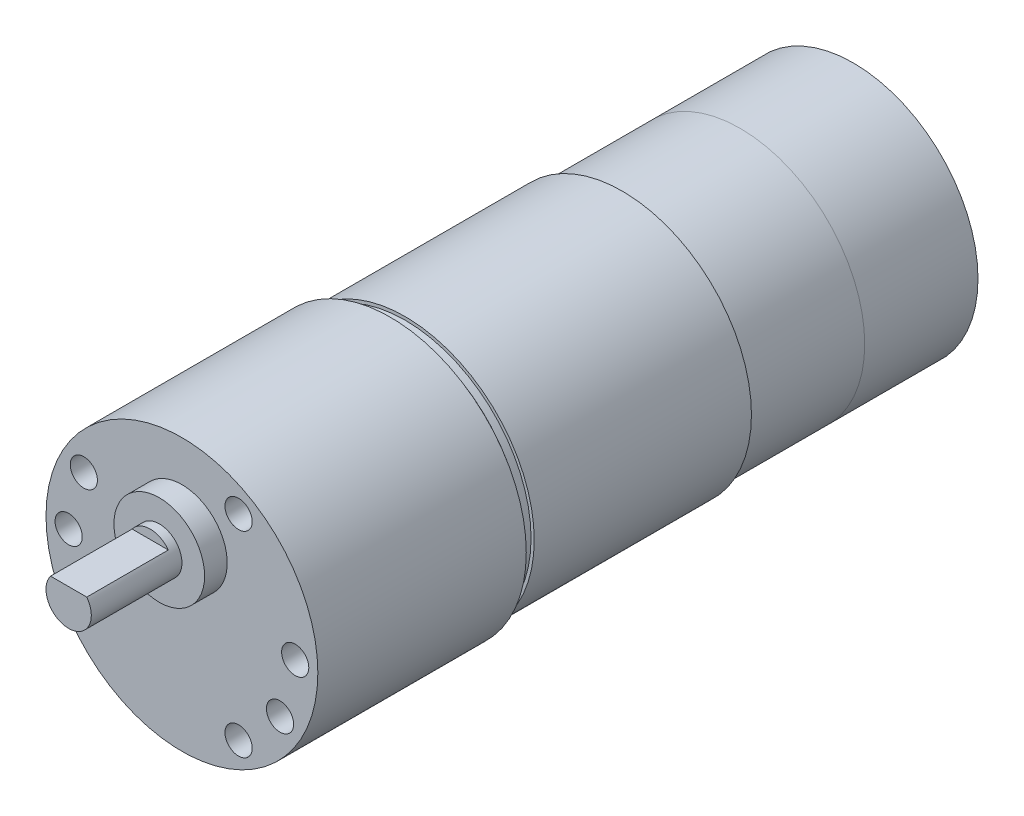
SolidWorks part; units mm, degrees
ref_plane "Спереди" through (0, 0, 0) normal (0, 0, 1) x (1, 0, 0)
ref_plane "Сверху" through (0, 0, 0) normal (0, 1, 0) x (1, 0, 0)
ref_plane "Справа" through (0, 0, 0) normal (1, 0, 0) x (0, 0, -1)
sketch "Эскиз2" plane through (0, 0, 0) normal (1, 0, 0) x (0, 0, -1)
  line L0 (0, 0) -> (0, 15)
  line L1 (0, 15) -> (23, 15)
  line L2 (23, 15) -> (23, 13.1609)
  line L3 (23, 13.1609) -> (23.8, 13.1609)
  line L4 (23.8, 13.1609) -> (23.8, 13.9002)
  line L5 (23.8, 13.9002) -> (24.6292, 13.9002)
  line L6 (24.6292, 13.9002) -> (24.6292, 14.25)
  line L7 (24.6292, 14.25) -> (48.6, 14.25)
  line L8 (61.6, 13.75) -> (61.6, 0)
  line L9 (48.6, 14.25) -> (48.6, 13.75)
  line L10 (48.6, 13.75) -> (61.6, 13.75)
  line L11 (0, 0) -> (61.6, 0)
  dimension "D1" = 23
  dimension "D2" = 15
  dimension "D3" = 38.6
  dimension "D4" = 13
  dimension "D5" = 0.8
  dimension "D6" = 14.25
  dimension "D7" = 13.75
revolve "Повернуть1" add sketch "Эскиз2" angle 360 about L11
sketch "Эскиз3" plane through (0, 0, -61.6) normal (0, 0, -1) x (-1, 0, 0)
  circle A0 centre (0, 0) radius 13.75
extrude "Бобышка-Вытянуть1" add sketch "Эскиз3" along normal blind 12.5 separate body
sketch "Эскиз4" plane through (0, 0, 0) normal (0, 0, 1) x (1, 0, 0)
  line L0 (0, 0) -> (6.25, 10.8253) construction
  line L1 (0, 0) -> (12.5, 0) construction
  line L2 (-11.225, 5.5) -> (-9.5263, 5.5) construction
  line L3 (0, 0) -> (0, 0.3653) construction
  line L4 (0, 0) -> (0, 12.5) construction
  line L5 (0, 0) -> (10.8253, 6.25) construction
  line L6 (0, 0) -> (-10.8253, 6.25) construction
  line L7 (0, 0) -> (-12.5, 0) construction
  line L8 (0, 0) -> (10.8253, -6.25) construction
  line L9 (0, 0) -> (6.25, -10.8253) construction
  line L10 (0, 5.5) -> (11.225, 5.5) construction
  circle A0 centre (0, 0) radius 12.5 construction
  circle A1 centre (-12.5, 0) radius 1.5
  circle A2 centre (-10.8253, 6.25) radius 1.5
  circle A3 centre (6.25, 10.8253) radius 1.5
  circle A4 centre (12.5, 0) radius 1.5
  circle A5 centre (10.8253, -6.25) radius 1.5
  circle A6 centre (6.25, -10.8253) radius 1.5
  dimension "D1" = 60
  dimension "D2" = 5.5
  dimension "D3" = 30
  dimension "D4" = 150
  dimension "D5" = 30
  dimension "D6" = 60
extrude "Вырез-Вытянуть1" cut sketch "Эскиз4" against normal blind 4
sketch "Эскиз5" plane through (0, 0, 0) normal (0, 0, 1) x (1, 0, 0)
  circle A0 centre (0, 5.5) radius 5
extrude "Бобышка-Вытянуть2" add sketch "Эскиз5" along normal blind 2.5
sketch "Эскиз6" plane through (0, 0, 2.5) normal (0, 0, 1) x (1, 0, 0)
  circle A0 centre (0, 5.5) radius 2.5
extrude "Бобышка-Вытянуть3" add sketch "Эскиз6" along normal blind 10
sketch "Эскиз7" plane through (0, 0, 12.5) normal (0, 0, 1) x (1, 0, 0)
  line L0 (-2.6405, 7) -> (2.8282, 7)
  line L1 (2.8282, 7) -> (2.8282, 8.8229)
  line L2 (2.8282, 8.8229) -> (-1.5136, 8.8229)
  line L3 (-1.5136, 8.8229) -> (-2.6405, 7)
  dimension "D1" = 1.5
extrude "Вырез-Вытянуть2" cut sketch "Эскиз7" against normal blind 9
